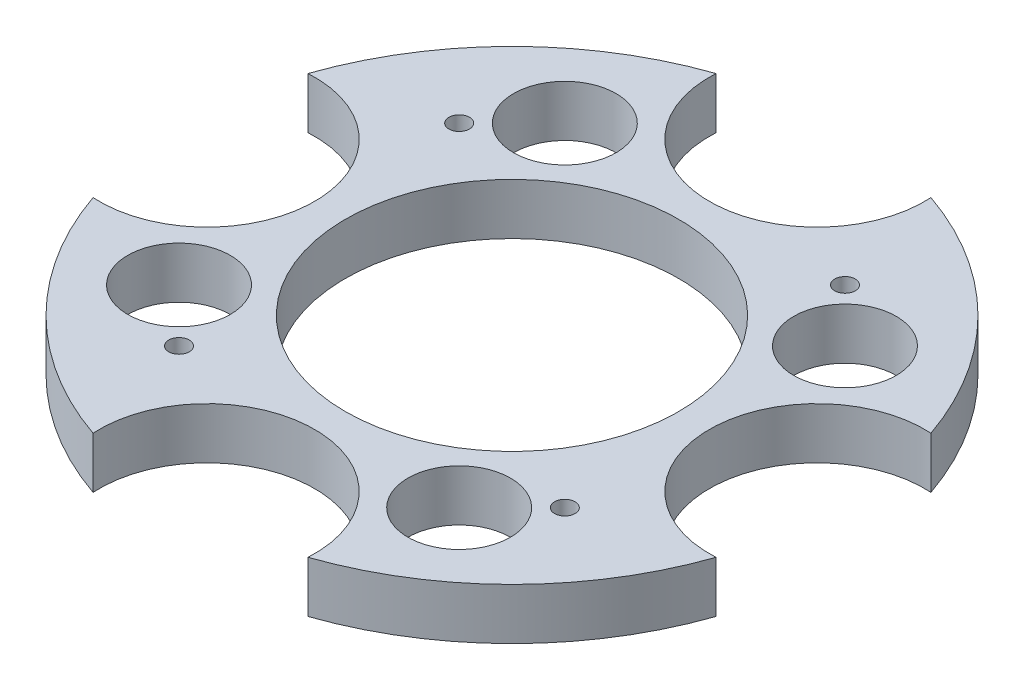
SolidWorks part; units mm, degrees
ref_plane "Front Plane" through (0, 0, 0) normal (0, 0, 1) x (1, 0, 0)
ref_plane "Top Plane" through (0, 0, 0) normal (0, 1, 0) x (1, 0, 0)
ref_plane "Right Plane" through (0, 0, 0) normal (1, 0, 0) x (0, 0, -1)
sketch "Sketch1" plane through (0, 0, 0) normal (0, 1, 0) x (1, 0, 0)
  circle A0 centre (0, 0) radius 32.135
  circle A1 centre (0, 0) radius 16.25
  dimension "D1" = 64.27
  dimension "D2" = 32.5
extrude "Boss-Extrude1" add sketch "Sketch1" along normal mid plane 5
sketch "Sketch2" plane through (0, 2.5, 0) normal (0, 1, 0) x (1, 0, 0)
  line L0 (0, 16.25) -> (0, 19.25) construction
  circle A0 centre (0, 29.75) radius 10.5
  circle A3 centre (0, 0) radius 16.25 construction
  dimension "D1" = 21
  dimension "D2" = 3
extrude "Cut-Extrude1" cut sketch "Sketch2" against normal through all
pattern_circular "CirPattern1" count 4 over 360 about axis through (0, 0, 0) along (0, 1, 0) of "Cut-Extrude1"
sketch "Sketch3" plane through (0, 2.5, 0) normal (0, 1, 0) x (1, 0, 0)
  arc A0 (-10.4812, 30.3777) -> (10.4812, 30.3777) centre (0, 29.75) cw
  arc A1 (-10.4812, 30.3777) -> (10.4812, 30.3777) centre (0, 29.75) ccw construction
  arc A2 (-12.6126, 34.5638) -> (12.6126, 34.5638) centre (0, 29.75) cw
  arc A3 (-12.6126, 34.5638) -> (-19.2914, 25.7002) centre (-31.2979, 41.6953) cw
  arc A4 (-10.4812, 30.3777) -> (-30.3777, 10.4812) centre (0, 0) ccw construction
  arc A5 (-19.2914, 25.7002) -> (-10.4812, 30.3777) centre (0, 0) cw
  arc A6 (10.4812, 30.3777) -> (19.2914, 25.7002) centre (0, 0) cw
  arc A7 (30.3777, 10.4812) -> (10.4812, 30.3777) centre (0, 0) ccw construction
  arc A8 (19.2914, 25.7002) -> (12.6126, 34.5638) centre (31.2979, 41.6953) cw
  dimension "D1" = 3
  dimension "D2" = 20
extrude "Boss-Extrude2" add sketch "Sketch3" against normal through all
pattern_circular "CirPattern2" count 4 over 360 about axis through (0, 0, 0) along (0, 1, 0) of "Boss-Extrude2"
sketch "Sketch4" plane through (0, 2.5, 0) normal (0, 1, 0) x (1, 0, 0)
  line L0 (-16.896, 30.8538) -> (-7.5226, 19.1456) construction
  line L1 (-9.7581, 21.9379) -> (-8.1968, 23.1878) construction
  line L2 (-9.3523, 24.6311) -> (-15.3864, 32.1683) construction
  line L3 (-26.2913, 0.9907) -> (-12.7442, 10.8281) construction
  line L4 (-9.5483, 13.1489) -> (-10.7234, 14.7672) construction
  line L5 (-12.8867, 13.1964) -> (-19.6602, 8.2777) construction
  line L6 (-13.6614, 18.813) -> (13.6614, 18.813) construction
  circle A0 centre (-13.6614, 18.813) radius 5
  circle A1 centre (0, 29.75) radius 10.5 construction
  circle A2 centre (0, 0) radius 16.25 construction
  circle A3 centre (13.6614, 18.813) radius 1
  point P21 (0, 18.813)
  dimension "D1" = 10
  dimension "D3" = 2
  dimension "D2" = 2
extrude "Cut-Extrude2" cut sketch "Sketch4" against normal through all
pattern_circular "CirPattern3" count 4 over 360 about axis through (0, 0, 0) along (0, 1, 0) of "Cut-Extrude2"
sketch "Sketch5" plane through (0, 2.5, 0) normal (0, 1, 0) x (1, 0, 0)
  circle A0 centre (0, 0) radius 32.135
  circle A1 centre (0, 0) radius 43.25
  arc A2 (-19.2914, 25.7002) -> (-25.7002, 19.2914) centre (0, 0) ccw construction
  arc A3 (-34.5638, 12.6126) -> (-34.5638, -12.6126) centre (-29.75, 0) ccw construction
extrude "Cut-Extrude3" cut sketch "Sketch5" against normal through all
